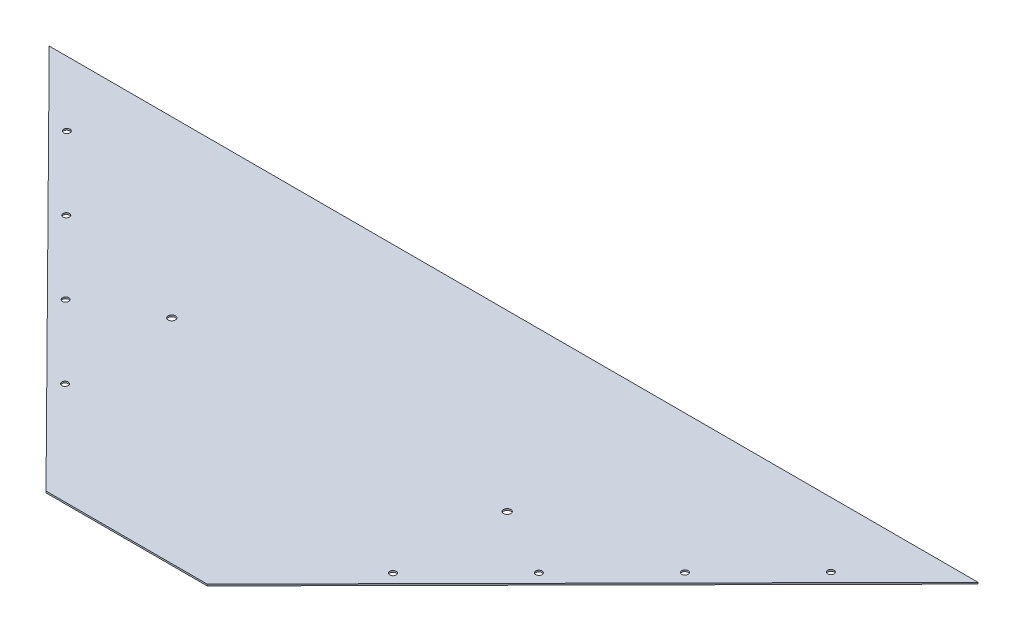
SolidWorks part; units mm, degrees
ref_plane "Front Plane" through (0, 0, 0) normal (0, 0, 1) x (1, 0, 0)
ref_plane "Top Plane" through (0, 0, 0) normal (0, 1, 0) x (1, 0, 0)
ref_plane "Right Plane" through (0, 0, 0) normal (1, 0, 0) x (0, 0, -1)
sketch "Sketch1" plane through (0, 0, 0) normal (0, 1, 0) x (1, 0, 0)
  line L0 (0, 0) -> (317.5, 0)
  line L1 (1073.15, 762) -> (317.5, 0)
  line L3 (1073.15, 762) -> (-755.65, 762)
  line L5 (-755.65, 762) -> (0, 0)
  line L6 (158.75, 762) -> (158.75, 0) construction
  dimension "D1" = 317.5
  dimension "D2" = 1073.15
  dimension "D4" = 1828.8
extrude "Boss-Extrude1" add sketch "Sketch1" along normal blind 3.175
sketch "Sketch2" plane through (0, 3.175, 0) normal (0, 1, 0) x (1, 0, 0)
  line L0 (-171.45, 419.1) -> (488.95, 419.1) construction
  line L1 (158.75, 419.1) -> (158.75, 0) construction
  line L2 (0, 0) -> (317.5, 0) construction
  line L3 (1073.15, 762) -> (-755.65, 762) construction
  circle A0 centre (-171.45, 419.1) radius 7.1437
  circle A1 centre (488.95, 419.1) radius 7.1437
  dimension "D2" = 14.2875
  dimension "D1" = 660.4
  dimension "D3" = 342.9
extrude "Cut-Extrude1" cut sketch "Sketch2" against normal up to next
sketch "Sketch3" plane through (0, 3.175, 0) normal (0, 1, 0) x (1, 0, 0)
  line L1 (-755.65, 762) -> (0, 0) construction
  line L2 (158.75, 762) -> (158.75, 0) construction
  line L3 (1073.15, 762) -> (-755.65, 762) construction
  line L4 (0, 0) -> (317.5, 0) construction
  circle A0 centre (-593.402, 634.4609) radius 6.35
  circle A1 centre (-450.3204, 490.1768) radius 6.35
  circle A2 centre (-307.2387, 345.8928) radius 6.35
  circle A3 centre (-164.157, 201.6088) radius 6.35
  circle A6 centre (481.657, 201.6088) radius 6.35
  circle A7 centre (624.7387, 345.8928) radius 6.35
  circle A8 centre (767.8204, 490.1768) radius 6.35
  circle A9 centre (910.902, 634.4609) radius 6.35
  dimension "D1" = 25.4
  dimension "D2" = 206.375
  dimension "D3" = 4
extrude "Cut-Extrude2" cut sketch "Sketch3" against normal through all
